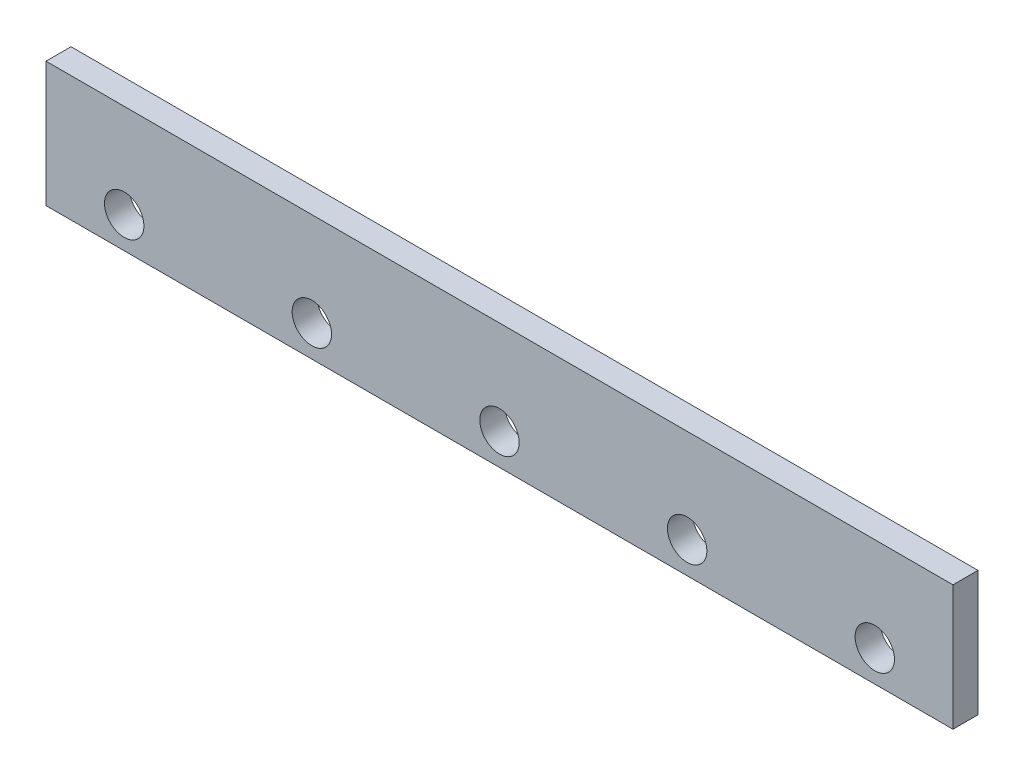
SolidWorks part; units mm, degrees
ref_plane "Front Plane" through (0, 0, 0) normal (0, 0, 1) x (1, 0, 0)
ref_plane "Top Plane" through (0, 0, 0) normal (0, 1, 0) x (1, 0, 0)
ref_plane "Right Plane" through (0, 0, 0) normal (1, 0, 0) x (0, 0, -1)
sketch "Sketch1" plane through (0, 0, 0) normal (0, 0, 1) x (1, 0, 0)
  line L1 (0, 0) -> (580, 0)
  line L2 (0, 0) -> (0, 80)
  line L3 (0, 80) -> (580, 80)
  line L4 (580, 0) -> (580, 80)
  dimension "D1" = 580
  dimension "D2" = 80
extrude "Boss-Extrude1" add sketch "Sketch1" along normal blind 16
sketch "Sketch2" plane through (0, 0, 16) normal (0, 0, 1) x (1, 0, 0)
  line L0 (50, 20) -> (50, 0) construction
  line L1 (0, 0) -> (580, 0) construction
  line L2 (50, 20) -> (664.212, 20) construction
  line L3 (50, 20) -> (0, 20) construction
  line L4 (0, 80) -> (0, 0) construction
  circle A0 centre (50, 20) radius 12.6
  circle A1 centre (170, 20) radius 12.6
  circle A2 centre (290, 20) radius 12.6
  circle A3 centre (410, 20) radius 12.6
  circle A4 centre (530, 20) radius 12.6
  dimension "D2" = 12.6
  dimension "D3" = 12.6
  dimension "D1" = 50
  dimension "D4" = 4
extrude "Cut-Extrude1" cut sketch "Sketch2" against normal blind 16
